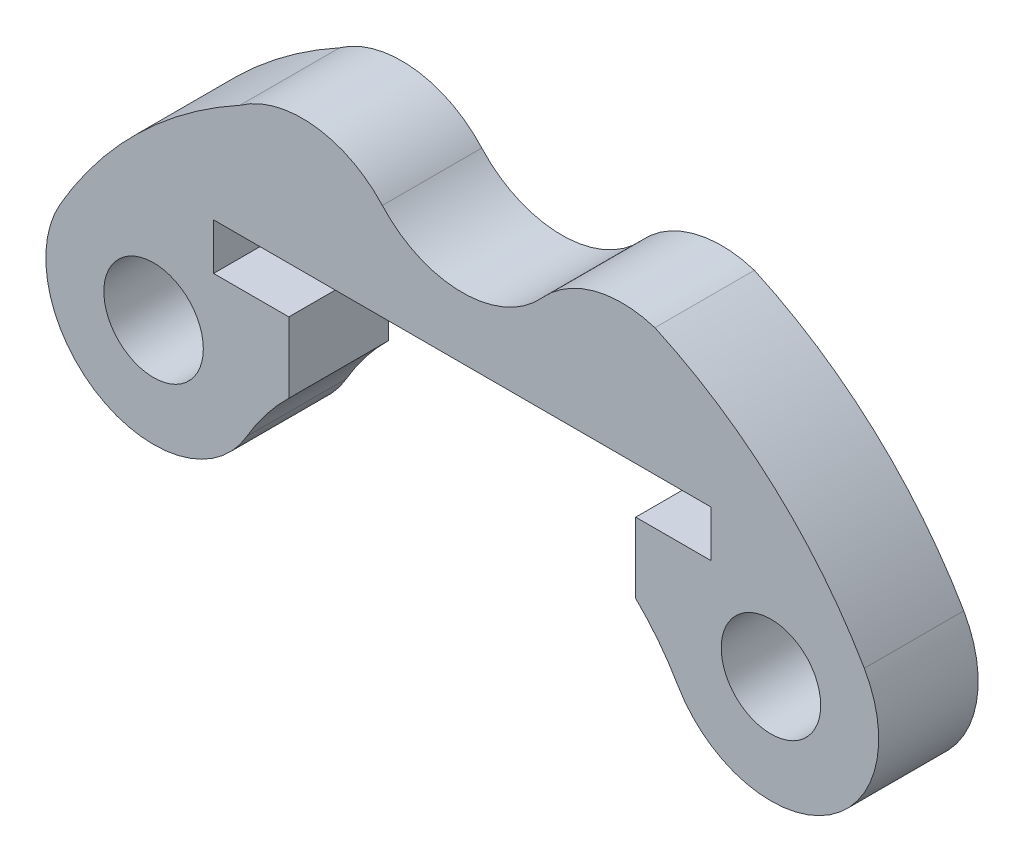
SolidWorks part; units mm, degrees
ref_plane "Plan de face" through (0, 0, 0) normal (0, 0, 1) x (1, 0, 0)
ref_plane "Plan de dessus" through (0, 0, 0) normal (0, 1, 0) x (1, 0, 0)
ref_plane "Plan de droite" through (0, 0, 0) normal (1, 0, 0) x (0, 0, -1)
sketch "Esquisse1" plane through (0, 0, 0) normal (0, 0, 1) x (1, 0, 0)
  line L0 (9.3098, 5.375) -> (7.6848, 2.5604) construction
  line L1 (5.2306, 7.5) -> (7.5, 7.5)
  line L2 (-9.3098, 5.375) -> (9.3098, 5.375) construction
  line L3 (-5.2306, 7.5) -> (-7.5, 7.5)
  line L4 (-7.6848, 2.5604) -> (-9.3098, 5.375) construction
  line L5 (-7.5, 7.5) -> (-7.5, 8.9)
  line L7 (7.5, 8.9) -> (7.5, 7.5)
  line L8 (7.5, 8.9) -> (-7.5, 8.9)
  line L9 (-5.2306, 5.375) -> (-5.2306, 7.5)
  line L10 (5.2306, 5.375) -> (5.2306, 7.5)
  arc A12 (-2.411, 11.8207) -> (2.411, 11.8207) centre (0, 14) ccw
  arc A16 (5.8094, 12.7378) -> (2.411, 11.8207) centre (4.8221, 9.6414) ccw
  arc A17 (-2.411, 11.8207) -> (-6.7074, 12.2887) centre (-4.8221, 9.6414) ccw
  arc A18 (-6.7074, 12.2887) -> (-12.1244, 7) centre (0, 0) ccw
  arc A28 (12.1244, 7) -> (5.8094, 12.7378) centre (0, 0) ccw
  arc A30 (10.4906, 2.3471) -> (-10.4906, 2.3471) centre (0, 0) ccw construction
  circle A31 centre (9.3098, 5.375) radius 1.5
  circle A33 centre (-9.3098, 5.375) radius 1.5
  arc A34 (6.4952, 3.75) -> (12.1244, 7) centre (9.3098, 5.375) ccw
  arc A35 (-12.1244, 7) -> (-6.4952, 3.75) centre (-9.3098, 5.375) ccw
  arc A37 (6.4952, 3.75) -> (5.2306, 5.375) centre (0, 0) ccw
  arc A38 (-5.2306, 5.375) -> (-6.4952, 3.75) centre (0, 0) ccw
  arc A39 (6.4952, 3.75) -> (-6.4952, 3.75) centre (0, 0) ccw construction
  point P31 (0, 0)
  dimension "D3" = 6.5
  dimension "D5" = 1.4
  dimension "D8" = 14
  dimension "D9" = 3.25
  dimension "D10" = 6.5
  dimension "D11" = 3.25
  dimension "D7" = 60
  dimension "D14" = 10.78
  dimension "D15" = 10.78
extrude "Boss.-Extru.2" add sketch "Esquisse1" along normal blind 3
